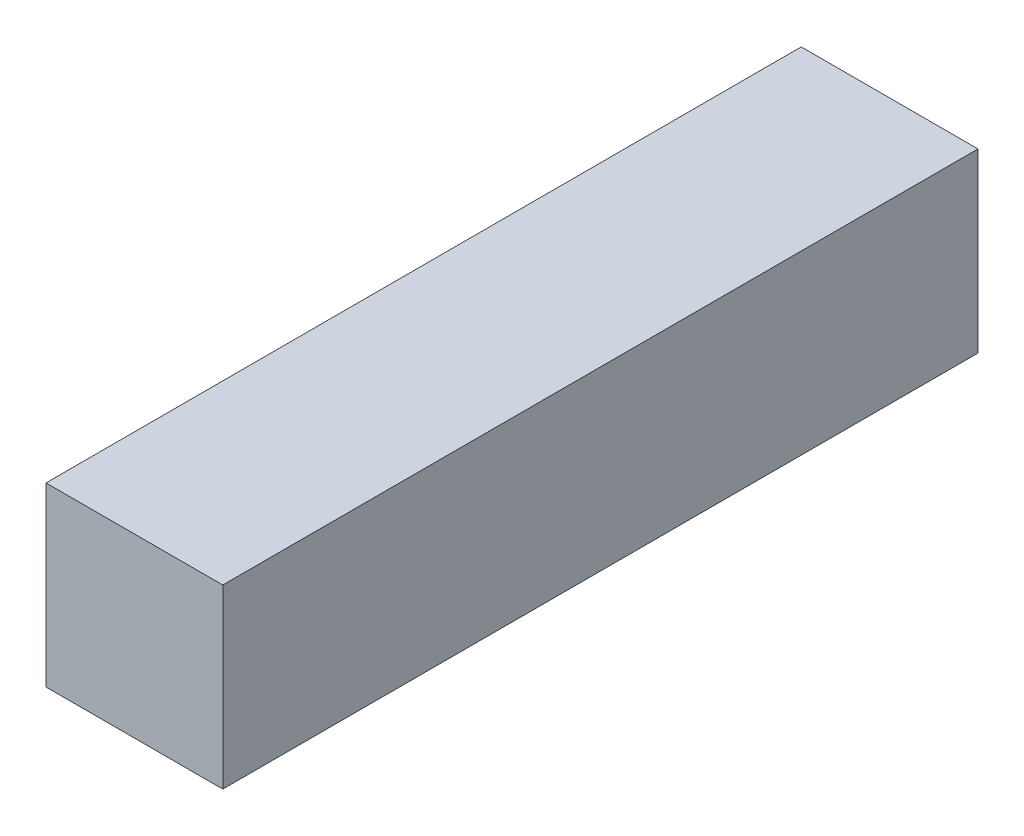
SolidWorks part; units mm, degrees
ref_plane "Спереди" through (0, 0, 0) normal (0, 0, 1) x (1, 0, 0)
ref_plane "Сверху" through (0, 0, 0) normal (0, 1, 0) x (1, 0, 0)
ref_plane "Справа" through (0, 0, 0) normal (1, 0, 0) x (0, 0, -1)
sketch "Эскиз1" plane through (0, 0, 0) normal (0, 1, 0) x (1, 0, 0)
  line L1 (-13.95, 59.6) -> (13.95, 59.6)
  line L2 (-13.95, 59.6) -> (-13.95, -59.6)
  line L3 (-13.95, -59.6) -> (13.95, -59.6)
  line L4 (13.95, 59.6) -> (13.95, -59.6)
  line L5 (-13.95, 59.6) -> (13.95, -59.6) construction
  line L6 (-13.95, -59.6) -> (13.95, 59.6) construction
  point P0 (0, 0)
extrude "Бобышка-Вытянуть1" add sketch "Эскиз1" along normal blind 27.9
